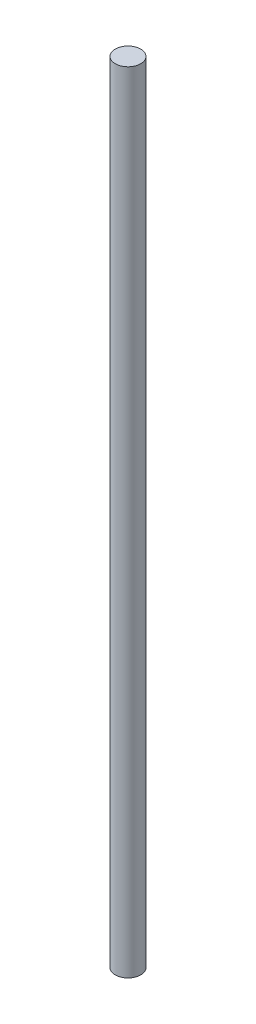
SolidWorks part; units mm, degrees
ref_plane "Front Plane" through (0, 0, 0) normal (0, 0, 1) x (1, 0, 0)
ref_plane "Top Plane" through (0, 0, 0) normal (0, 1, 0) x (1, 0, 0)
ref_plane "Right Plane" through (0, 0, 0) normal (1, 0, 0) x (0, 0, -1)
sketch "Sketch1" plane through (0, 0, 0) normal (0, 1, 0) x (1, 0, 0)
  circle A0 centre (0, 0) radius 2.5
  dimension "D1" = 5
extrude "Boss-Extrude1" add sketch "Sketch1" along normal blind 155
